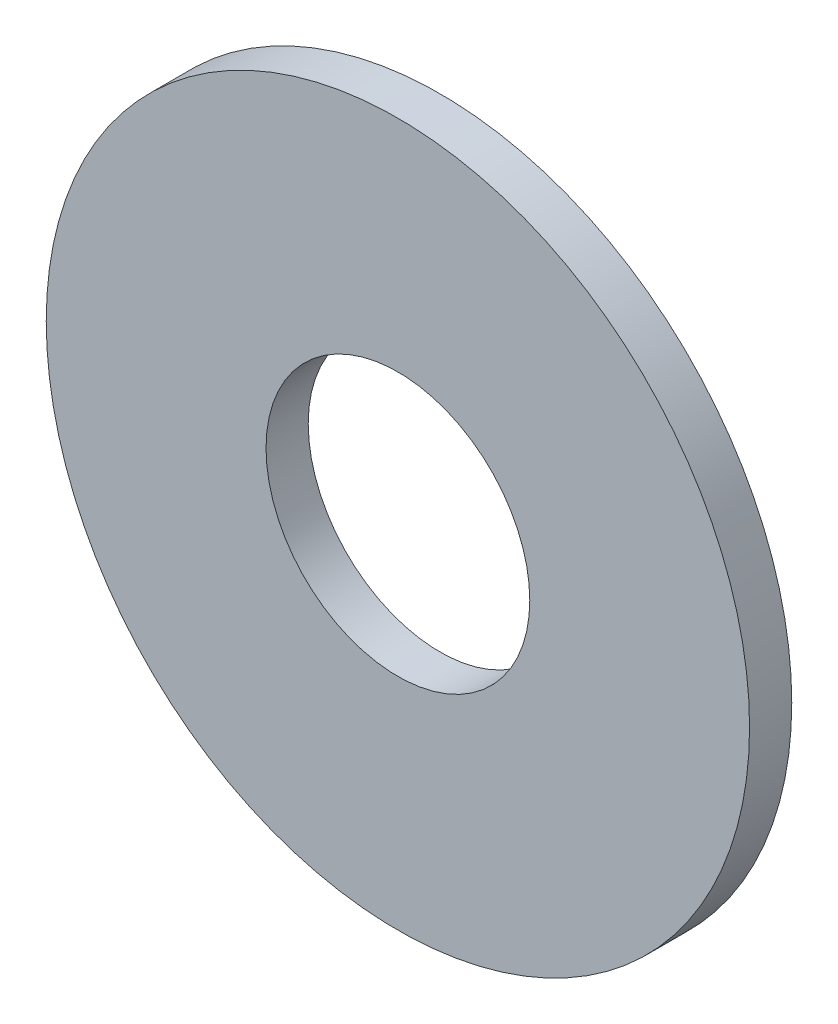
SolidWorks part; units mm, degrees
material "AISI 1020"
ref_plane "Front Plane" through (0, 0, 0) normal (0, 0, 1) x (1, 0, 0)
ref_plane "Top Plane" through (0, 0, 0) normal (0, 1, 0) x (1, 0, 0)
ref_plane "Right Plane" through (0, 0, 0) normal (1, 0, 0) x (0, 0, -1)
sketch "Sketch1" plane through (0, 0, 0) normal (0, 0, 1) x (1, 0, 0)
  circle A0 centre (0, 0) radius 2.3813
  circle A1 centre (0, 0) radius 6.35
  dimension "ID" = 4.7625
  dimension "OD" = 12.7
extrude "Extrude1" add sketch "Sketch1" against normal blind 0.762
